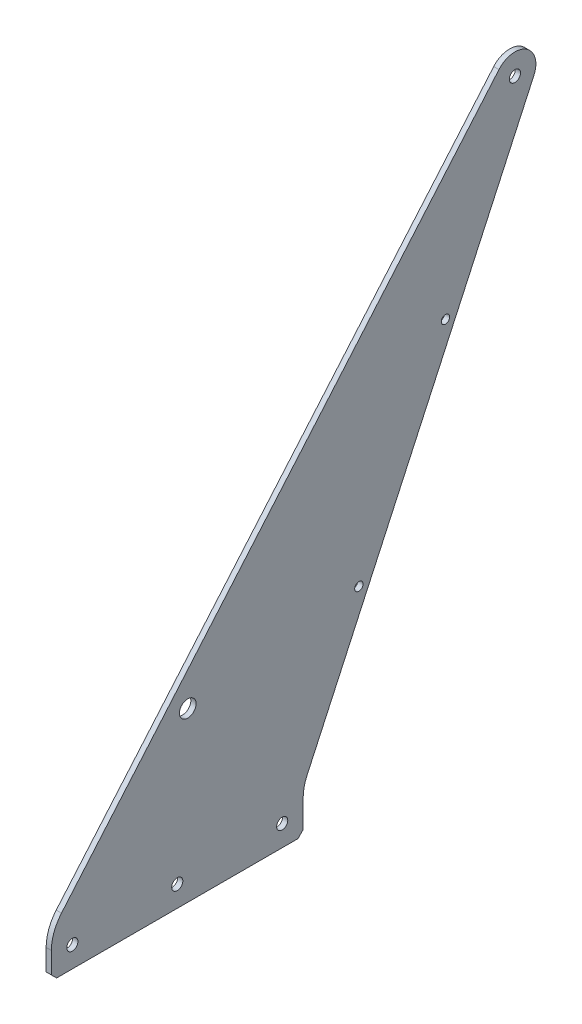
SolidWorks part; units mm, degrees
material "6061-T6 (SS)"
ref_plane "Front" through (0, 0, 0) normal (0, 0, 1) x (1, 0, 0)
ref_plane "Top" through (0, 0, 0) normal (0, 1, 0) x (1, 0, 0)
ref_plane "Right" through (0, 0, 0) normal (1, 0, 0) x (0, 0, -1)
sketch "Sketch1" plane through (0, 0, 0) normal (1, 0, 0) x (0, 0, -1)
  line L5 (82.55, 101.6) -> (-348.9452, 11.9126) construction
  line L6 (82.55, 101.6) -> (-7.1374, 533.0952) construction
  line L7 (280.5654, 334.0693) -> (88.8114, 173.1687) construction
  line L8 (88.8114, 173.1687) -> (10.9813, 107.8614) construction
  line L9 (82.55, 101.6) -> (10.9813, 107.8614) construction
  line L10 (10.9813, 107.8614) -> (15.1928, 87.5996) construction
  line L11 (82.55, 101.6) -> (88.8114, 173.1687) construction
  line L12 (88.8114, 173.1687) -> (68.5496, 168.9572) construction
  circle A0 centre (82.55, 101.6) radius 5.0419
  dimension "D1" = 10.0838
  dimension "D3" = 82.55
  dimension "D2" = 101.6
  dimension "D4" = 40
  dimension "D7" = 89.6874
  dimension "D8" = 431.4952
  dimension "D9" = 90
  dimension "D10" = 101.6
  dimension "D11" = 250.317
sketch "Sketch2" plane through (0, 0, 0) normal (1, 0, 0) x (0, 0, -1)
  line L0 (0, 0) -> (0, 25.4)
  line L2 (0, 0) -> (152.4, 0)
  line L3 (152.4, 0) -> (152.4, 25.4)
  line L4 (152.4, 25.4) -> (292.101, 328.757)
  line L6 (0, 25.4) -> (270.9118, 342.3215)
  arc A0 (292.101, 328.757) -> (270.9118, 342.3215) centre (280.5654, 334.0693) ccw
  circle A2 centre (82.55, 101.6) radius 5.0419 construction
  circle A3 centre (82.55, 101.6) radius 5.0419
  circle A4 centre (280.5654, 334.0693) radius 3.3782
  dimension "D3" = 12.7
  dimension "D4" = 6.7564
  dimension "D1" = 25.4
  dimension "D2" = 152.4
extrude "Boss-Extrude2" add sketch "Sketch2" along normal blind 3.175
sketch "Sketch3" plane through (3.175, 0, 0) normal (1, 0, 0) x (0, 0, -1)
  line L0 (0, 0) -> (152.4, 0) construction
  line L1 (0, 25.4) -> (0, 0) construction
  line L2 (152.4, 0) -> (152.4, 25.4) construction
  line L3 (12.7, 12.7) -> (139.7, 12.7) construction
  line L4 (152.4, 25.4) -> (292.101, 328.757) construction
  line L5 (186.1192, 113.8011) -> (238.5265, 227.6022) construction
  line L6 (238.5265, 227.6022) -> (290.9338, 341.4033) construction
  line L7 (186.1192, 113.8011) -> (133.7119, 0) construction
  circle A0 centre (12.7, 12.7) radius 3.3782
  circle A1 centre (76.2, 12.7) radius 3.3782
  circle A2 centre (139.7, 12.7) radius 3.3782
  circle A3 centre (238.5265, 227.6022) radius 2.54
  circle A4 centre (186.1192, 113.8011) radius 2.54
  arc A5 (292.101, 328.757) -> (270.9118, 342.3215) centre (280.5654, 334.0693) ccw construction
  dimension "D1" = 12.7
  dimension "D2" = 12.7
  dimension "D3" = 12.7
  dimension "D4" = 6.7564
  dimension "D5" = 6.35
  dimension "D6" = 6.35
  dimension "D7" = 5.08
extrude "Cut-Extrude1" cut sketch "Sketch3" against normal through all
chamfer "Chamfer1" distance 3.175 angle 45 2 edges at (1.5875, 0, 0) (1.5875, 0, -152.4)
fillet "Fillet1" radius 25.4 2 edges at (1.5875, 25.4, -152.4) (1.5875, 25.4, 0)
